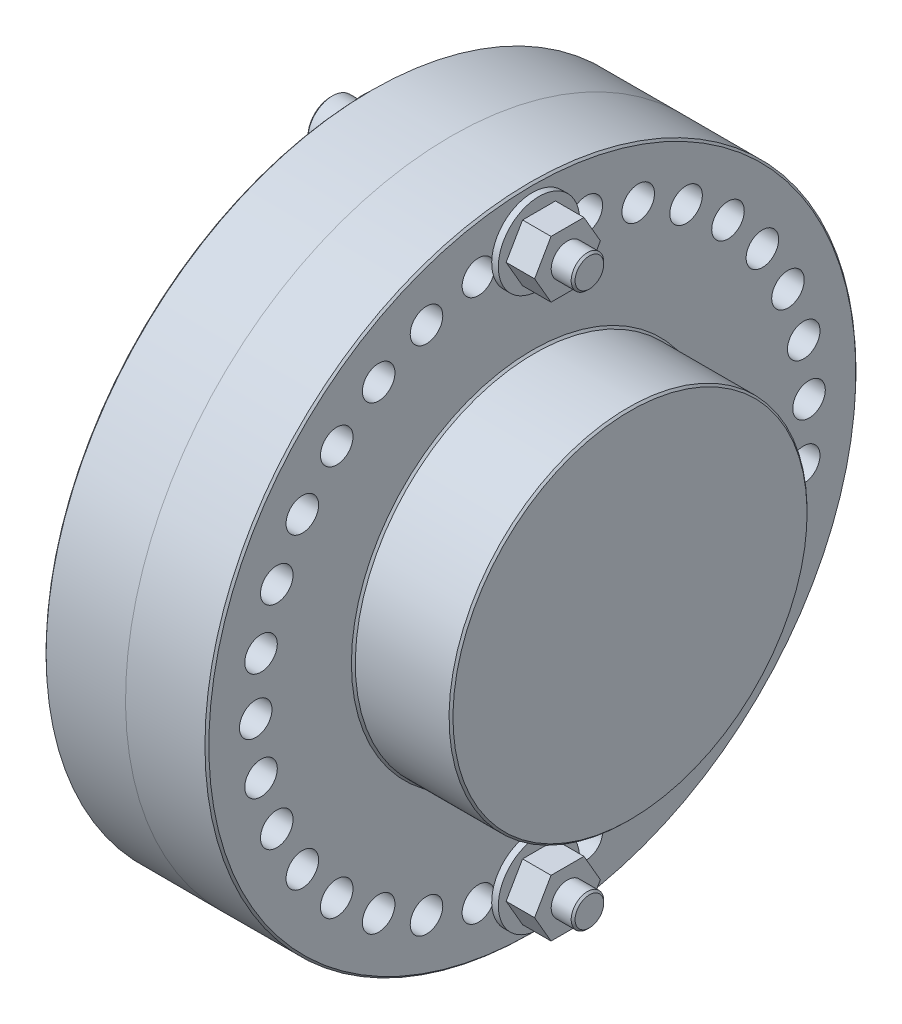
SolidWorks part; units mm, degrees
ref_plane "Front Plane" through (0, 0, 0) normal (0, 0, 1) x (1, 0, 0)
ref_plane "Top Plane" through (0, 0, 0) normal (0, 1, 0) x (1, 0, 0)
ref_plane "Right Plane" through (0, 0, 0) normal (1, 0, 0) x (0, 0, -1)
sketch "Sketch1" plane through (0, 0, 0) normal (0, 0, 1) x (1, 0, 0)
  line L0 (0, 0) -> (-34.925, 0) construction
  line L1 (0, 0) -> (0, 63.5)
  line L2 (0, 63.5) -> (-15.875, 63.5)
  line L3 (-15.875, 63.5) -> (-15.875, 34.925)
  line L4 (-15.875, 34.925) -> (-34.925, 34.925)
  line L5 (-34.925, 34.925) -> (-34.925, 0)
  line L6 (-34.925, 0) -> (0, 0)
  line L7 (0, 0) -> (-58.9413, 0) construction
  dimension "Dim K" = 34.925
  dimension "Dim A" = 127
  dimension "Dim E" = 15.875
  dimension "Dim C" = 69.85
revolve "Revolve1" add sketch "Sketch1" angle 360 about L7
chamfer "Chamfer2" distance 0.381 angle 45 3 edges at (-34.925, 34.925, 0) (-15.875, 63.5, 0) (-15.875, 34.925, 0)
mirror "Mirror1" about plane through (0, 0, 0) normal (1, 0, 0) of bodies 101
sketch "Sketch2" plane through (-15.875, 0, 0) normal (-1, 0, 0) x (0, 0, 1)
  line L0 (0, 53.975) -> (0, 0) construction
  circle A0 centre (0, 53.975) radius 3.175
  circle A1 centre (0, 0) radius 53.975 construction
  circle A2 centre (9.9179, 53.056) radius 3.175
  circle A3 centre (19.498, 50.3302) radius 3.175
  circle A4 centre (28.4142, 45.8905) radius 3.175
  circle A5 centre (36.3627, 39.888) radius 3.175
  circle A6 centre (43.073, 32.5272) radius 3.175
  circle A7 centre (48.3164, 24.0587) radius 3.175
  circle A8 centre (51.9145, 14.771) radius 3.175
  circle A9 centre (53.7448, 4.9802) radius 3.175
  circle A10 centre (53.7448, -4.9802) radius 3.175
  circle A11 centre (51.9145, -14.771) radius 3.175
  circle A12 centre (48.3164, -24.0587) radius 3.175
  circle A13 centre (43.073, -32.5272) radius 3.175
  circle A14 centre (36.3627, -39.888) radius 3.175
  circle A15 centre (28.4142, -45.8905) radius 3.175
  circle A16 centre (19.498, -50.3302) radius 3.175
  circle A17 centre (9.9179, -53.056) radius 3.175
  circle A18 centre (0, -53.975) radius 3.175
  circle A19 centre (-9.9179, -53.056) radius 3.175
  circle A20 centre (-19.498, -50.3302) radius 3.175
  circle A21 centre (-28.4142, -45.8905) radius 3.175
  circle A22 centre (-36.3627, -39.888) radius 3.175
  circle A23 centre (-43.073, -32.5272) radius 3.175
  circle A24 centre (-48.3164, -24.0587) radius 3.175
  circle A25 centre (-51.9145, -14.771) radius 3.175
  circle A26 centre (-53.7448, -4.9802) radius 3.175
  circle A27 centre (-53.7448, 4.9802) radius 3.175
  circle A28 centre (-51.9145, 14.771) radius 3.175
  circle A29 centre (-48.3164, 24.0587) radius 3.175
  circle A30 centre (-43.073, 32.5272) radius 3.175
  circle A31 centre (-36.3627, 39.888) radius 3.175
  circle A32 centre (-28.4142, 45.8905) radius 3.175
  circle A33 centre (-19.498, 50.3302) radius 3.175
  circle A34 centre (-9.9179, 53.056) radius 3.175
  dimension "D1" = 34
  dimension "Dim H" = 107.95
  dimension "Dim D" = 6.35
extrude "Cut-Extrude1" cut sketch "Sketch2" against normal through all
sketch "Sketch3" plane through (15.875, 0, 0) normal (1, 0, 0) x (0, 0, -1)
  circle A0 centre (0, 53.975) radius 3.175 construction
  circle A1 centre (0, 53.975) radius 3.175
  circle A2 centre (10.53, 52.9379) radius 3.175
  circle A3 centre (20.6553, 49.8664) radius 3.175
  circle A4 centre (29.9869, 44.8786) radius 3.175
  circle A5 centre (38.1661, 38.1661) radius 3.175
  circle A6 centre (44.8786, 29.9869) radius 3.175
  circle A7 centre (49.8664, 20.6553) radius 3.175
  circle A8 centre (52.9379, 10.53) radius 3.175
  circle A9 centre (53.975, 0) radius 3.175
  circle A10 centre (52.9379, -10.53) radius 3.175
  circle A11 centre (49.8664, -20.6553) radius 3.175
  circle A12 centre (44.8786, -29.9869) radius 3.175
  circle A13 centre (38.1661, -38.1661) radius 3.175
  circle A14 centre (29.9869, -44.8786) radius 3.175
  circle A15 centre (20.6553, -49.8664) radius 3.175
  circle A16 centre (10.53, -52.9379) radius 3.175
  circle A17 centre (0, -53.975) radius 3.175
  circle A18 centre (-10.53, -52.9379) radius 3.175
  circle A19 centre (-20.6553, -49.8664) radius 3.175
  circle A20 centre (-29.9869, -44.8786) radius 3.175
  circle A21 centre (-38.1661, -38.1661) radius 3.175
  circle A22 centre (-44.8786, -29.9869) radius 3.175
  circle A23 centre (-49.8664, -20.6553) radius 3.175
  circle A24 centre (-52.9379, -10.53) radius 3.175
  circle A25 centre (-53.975, 0) radius 3.175
  circle A26 centre (-52.9379, 10.53) radius 3.175
  circle A27 centre (-49.8664, 20.6553) radius 3.175
  circle A28 centre (-44.8786, 29.9869) radius 3.175
  circle A29 centre (-38.1661, 38.1661) radius 3.175
  circle A30 centre (-29.9869, 44.8786) radius 3.175
  circle A31 centre (-20.6553, 49.8664) radius 3.175
  circle A32 centre (-10.53, 52.9379) radius 3.175
  circle A33 centre (0, -53.975) radius 3.175 construction
  dimension "D1" = 32
extrude "Cut-Extrude2" cut sketch "Sketch3" against normal through all
sketch "Sketch4" plane through (-15.875, 0, 0) normal (-1, 0, 0) x (0, 0, 1)
  circle A0 centre (0, 53.975) radius 3.5719
  circle A1 centre (0, 53.975) radius 7.9375
  dimension "Dim Washer OD" = 15.875
  dimension "Dim Washer ID" = 7.1437
extrude "Boss-Extrude1" add sketch "Sketch4" along normal blind 1.2954 separate body
mirror "Mirror2" about plane through (0, 0, 0) normal (1, 0, 0) of bodies 106
ref_plane "Plane1" through (27.0002, 0, 0) normal (1, 0, 0) x (0, 0, -1)
sketch "Sketch5" plane through (-17.1704, 0, 0) normal (-1, 0, 0) x (0, 0, 1)
  circle A0 centre (0, 53.975) radius 4.7625
  dimension "Dim head dia" = 9.525
extrude "Boss-Extrude2" add sketch "Sketch5" along normal blind 6.35 separate body
sketch "Sketch6" plane through (-23.5204, 0, 0) normal (-1, 0, 0) x (0, 0, 1)
  line L1 (0, 51.2254) -> (2.3812, 52.6002)
  line L2 (2.3812, 52.6002) -> (2.3812, 55.3498)
  line L3 (2.3812, 55.3498) -> (0, 56.7246)
  line L4 (0, 56.7246) -> (-2.3813, 55.3498)
  line L5 (-2.3813, 55.3498) -> (-2.3813, 52.6002)
  line L6 (-2.3813, 52.6002) -> (0, 51.2254)
  circle A0 centre (0, 53.975) radius 2.3812 construction
  dimension "Dim socket hex width" = 4.7625
extrude "Cut-Extrude3" cut sketch "Sketch6" against normal blind 4.7625
sketch "Sketch7" plane through (-17.1704, 0, 0) normal (1, 0, 0) x (0, 0, -1)
  circle A1 centre (0, 53.975) radius 3.175 construction
  circle A2 centre (0, 53.975) radius 3.175
extrude "Boss-Extrude4" add sketch "Sketch7" along normal up to surface (44.1706 mm away) up to plane "Plane1"
sketch "Sketch8" plane through (17.1704, 0, 0) normal (1, 0, 0) x (0, 0, -1)
  line L1 (3.2079, 59.5312) -> (-3.2079, 59.5312)
  line L2 (-3.2079, 59.5312) -> (-6.4158, 53.975)
  line L3 (-6.4158, 53.975) -> (-3.2079, 48.4187)
  line L4 (-3.2079, 48.4187) -> (3.2079, 48.4187)
  line L5 (3.2079, 48.4187) -> (6.4158, 53.975)
  line L6 (6.4158, 53.975) -> (3.2079, 59.5312)
  circle A0 centre (0, 53.975) radius 3.175
  circle A1 centre (0, 53.975) radius 3.175 construction
  circle A2 centre (0, 53.975) radius 5.5562 construction
  dimension "Dim nut width" = 11.1125
extrude "Boss-Extrude5" add sketch "Sketch8" along normal blind 5.5562 separate body
chamfer "Chamfer1" distance 0.381 angle 45 2 edges at (27.0002, 57.15, 0) (-23.5204, 49.2125, 0)
mirror "Mirror3" about plane through (0, 0, 0) normal (0, 1, 0) of bodies 112 111 107 106
